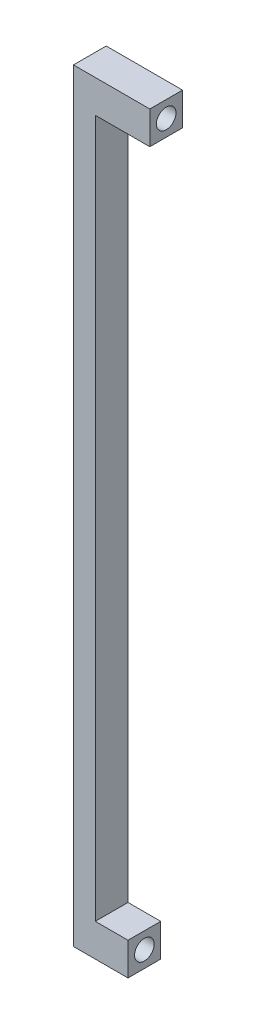
SolidWorks part; units mm, degrees
ref_plane "Alzado" through (0, 0, 0) normal (0, 0, 1) x (1, 0, 0)
ref_plane "Planta" through (0, 0, 0) normal (0, 1, 0) x (1, 0, 0)
ref_plane "Vista lateral" through (0, 0, 0) normal (1, 0, 0) x (0, 0, -1)
sketch "Croquis1" plane through (0, 0, 0) normal (0, 0, 1) x (1, 0, 0)
  line L1 (0, 0) -> (4, 0)
  line L2 (0, 0) -> (0, 140)
  line L3 (0, 140) -> (4, 140)
  line L4 (4, 0) -> (4, 140)
  line L5 (4, 140) -> (14, 140)
  line L6 (4, 140) -> (4, 134)
  line L7 (4, 134) -> (14, 134)
  line L8 (14, 140) -> (14, 134)
  line L9 (4, 0) -> (10, 0)
  line L10 (4, 0) -> (4, 6)
  line L11 (4, 6) -> (10, 6)
  line L12 (10, 0) -> (10, 6)
  point P11 (0, 0)
  point P12 (0, 0)
  point P13 (0, 0)
  point P14 (0, 0)
  point P15 (0, 0)
  point P16 (0, 0)
  dimension "D1" = 6
  dimension "D2" = 6
  dimension "D3" = 134
  dimension "D4" = 4
  dimension "D5" = 10
  dimension "D6" = 6
extrude "Saliente-Extruir1" add sketch "Croquis1" along normal blind 6 contours L8 L5 L4 L7 | L1 L4 L3 L2 | L9 L12 L11 L4
hole_wizard "Taladro de margen para M31" positions "Croquis2" profile "Croquis3" hole size "M3" standard "Ansi Metric"
sketch "Croquis2" plane through (14, 0, 0) normal (1, 0, 0) x (0, 0, -1)
  point P0 (-3, 137)
sketch "Croquis3" plane through (14, 137, 3) normal (0, 1, 0) x (0, 0, -1)
  line L0 (0, 0) -> (0, 4.0815)
  line L1 (0, 4.0815) -> (1.8, 3)
  line L2 (1.8, 3) -> (1.8, 0)
  line L5 (1.8, 0) -> (0, 0)
  line L10 (0, 4.0815) -> (-1.8, 3) construction
  line L11 (0, -6.35) -> (0, 107.95) construction
  dimension "Diámetro de taladro" = 3.6
  dimension "Profundidad de taladro" = 3
  dimension "Ángulo de perforador" = 118
hole_wizard "Taladro de margen para M32" positions "Croquis4" profile "Croquis5" hole size "M3" standard "Ansi Metric"
sketch "Croquis4" plane through (10, 0, 0) normal (1, 0, 0) x (0, 0, -1)
  point P0 (-3, 3)
sketch "Croquis5" plane through (10, 3, 3) normal (0, 1, 0) x (0, 0, -1)
  line L0 (0, 0) -> (0, 9.6815)
  line L1 (0, 9.6815) -> (1.8, 8.6)
  line L2 (1.8, 8.6) -> (1.8, 0)
  line L5 (1.8, 0) -> (0, 0)
  line L10 (0, 9.6815) -> (-1.8, 8.6) construction
  line L11 (0, -6.35) -> (0, 107.95) construction
  dimension "Diámetro de taladro" = 3.6
  dimension "Profundidad de taladro" = 8.6
  dimension "Ángulo de perforador" = 118
